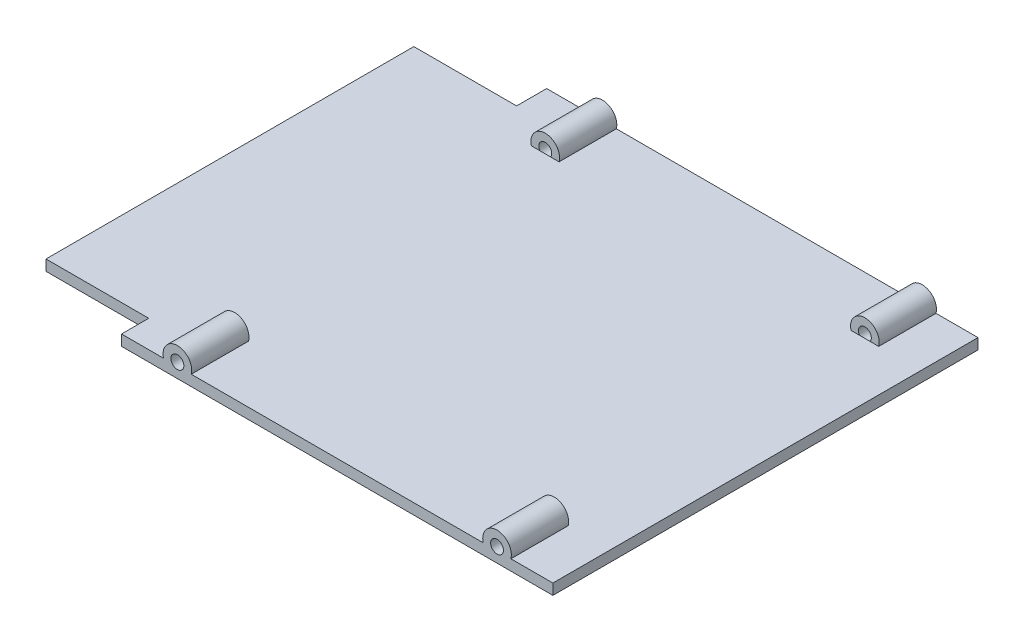
SolidWorks part; units mm, degrees
ref_plane "Front Plane" through (0, 0, 0) normal (0, 0, 1) x (1, 0, 0)
ref_plane "Top Plane" through (0, 0, 0) normal (0, 1, 0) x (1, 0, 0)
ref_plane "Right Plane" through (0, 0, 0) normal (1, 0, 0) x (0, 0, -1)
sketch "Sketch1" plane through (0, 0, 0) normal (0, 0, 1) x (1, 0, 0)
  line L0 (-567.145, -26.2672) -> (-567.145, -24.7672)
  line L2 (-567.145, -24.7672) -> (-506.895, -24.7672)
  line L4 (-506.895, -24.7672) -> (-506.895, -26.2672)
  line L5 (-506.895, -26.2672) -> (-567.145, -26.2672)
  line L8 (-391.345, -26.2672) -> (-583.345, -26.2672) construction
  line L9 (-506.695, -26.2672) -> (-506.695, 13.7328) construction
  line L10 (-567.345, 13.7328) -> (-567.345, -26.2672) construction
  dimension "D1" = 1.5
  dimension "D2" = 0.2
  dimension "D3" = 0.2
extrude "Boss-Extrude1" add sketch "Sketch1" against normal up to surface (59.38 mm away) from surface
sketch "Sketch2" plane through (-567.145, 0, 0) normal (-1, 0, 0) x (0, 0, 1)
  line L0 (-10.3874, -24.7672) -> (-10.3874, -26.2672)
  line L1 (-14.5874, -24.7672) -> (44.7926, -24.7672) construction
  line L2 (-14.5874, -26.2672) -> (44.7926, -26.2672) construction
  line L3 (-10.3874, -26.2672) -> (40.9926, -26.2672)
  line L4 (40.9926, -26.2672) -> (40.9926, -24.7672)
  line L5 (40.9926, -24.7672) -> (-10.3874, -24.7672)
  line L6 (-10.5874, -15.3672) -> (-10.5874, -26.2672) construction
  line L7 (40.7926, -15.3672) -> (40.7926, -26.2672) construction
  point P10 (-10.3874, -25.5172)
  dimension "D1" = 0.2
  dimension "D2" = 0.2
extrude "Boss-Extrude2" add sketch "Sketch2" along normal offset from surface (14.35 mm away) 0.2
sketch "Sketch3" plane through (0, 0, -14.5874) normal (0, 0, -1) x (-1, 0, 0)
  circle A0 centre (559.345, -24.2672) radius 2
  circle A1 centre (514.695, -24.2672) radius 2
extrude "Boss-Extrude3" add sketch "Sketch3" against normal blind 8
sketch "Sketch4" plane through (0, 0, -14.5874) normal (0, 0, -1) x (-1, 0, 0)
  circle A0 centre (559.345, -24.2672) radius 0.9
  circle A1 centre (514.695, -24.2672) radius 0.9
  dimension "D1" = 1.8
extrude "Cut-Extrude1" cut sketch "Sketch4" against normal blind 8
sketch "Sketch5" plane through (0, 0, 44.7926) normal (0, 0, 1) x (1, 0, 0)
  circle A0 centre (-559.345, -24.2672) radius 2
  circle A1 centre (-514.695, -24.2672) radius 2
extrude "Boss-Extrude4" add sketch "Sketch5" against normal blind 8
sketch "Sketch6" plane through (0, 0, 44.7926) normal (0, 0, 1) x (1, 0, 0)
  circle A0 centre (-514.695, -24.2672) radius 0.9
  circle A1 centre (-559.345, -24.2672) radius 0.9
  dimension "D1" = 1.8
extrude "Cut-Extrude2" cut sketch "Sketch6" against normal blind 8
